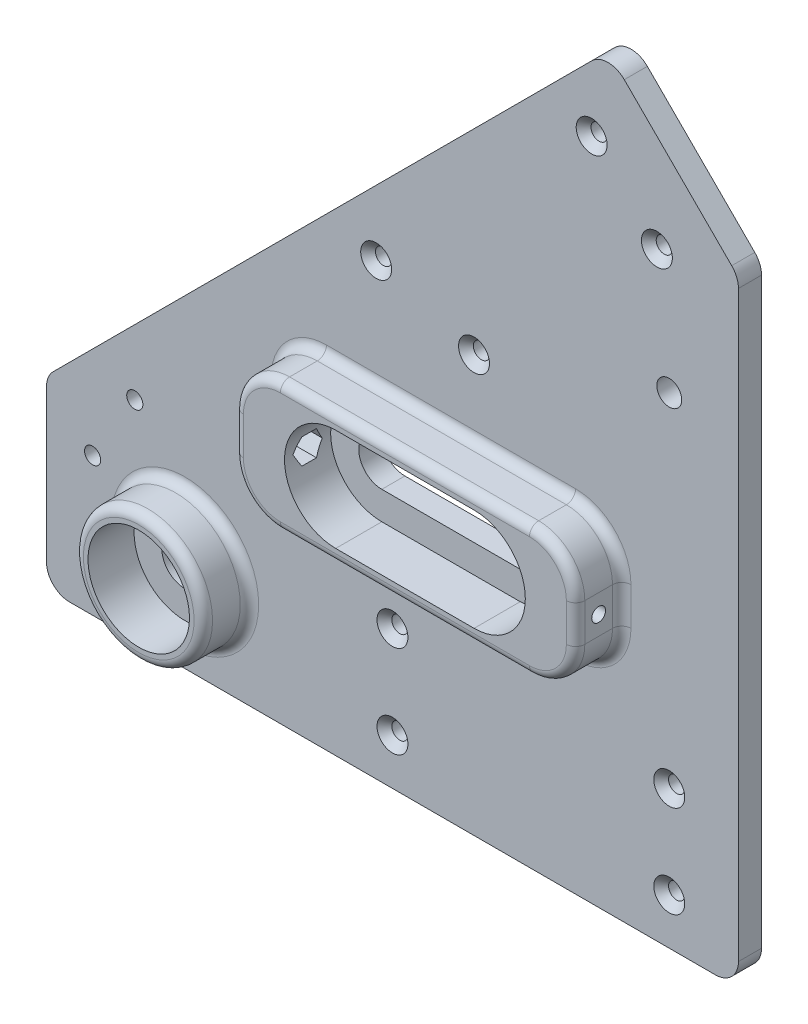
SolidWorks part; units mm, degrees
ref_plane "Front Plane" through (0, 0, 0) normal (0, 0, 1) x (1, 0, 0)
ref_plane "Top Plane" through (0, 0, 0) normal (0, 1, 0) x (1, 0, 0)
ref_plane "Right Plane" through (0, 0, 0) normal (1, 0, 0) x (0, 0, -1)
sketch "Sketch1" plane through (0, 0, 0) normal (0, 0, 1) x (1, 0, 0)
  line L0 (-75, 20) -> (46.7157, 141.7157)
  line L1 (-18.4315, 20) -> (75, 20) construction
  line L2 (-75, 20) -> (-75, -20)
  line L3 (-75, -20) -> (75, -20)
  line L4 (75, 20) -> (75, -20)
  line L5 (-75, 20) -> (75, -20) construction
  line L6 (-75, -20) -> (75, 20) construction
  line L7 (-75, -20) -> (75, -20)
  line L11 (46.7157, 141.7157) -> (75, 113.4315)
  line L12 (75, 113.4315) -> (-18.4315, 20) construction
  line L13 (-75, 0) -> (75, 0) construction
  line L14 (-75, 10) -> (75, 10) construction
  line L15 (-75, -10) -> (75, -10) construction
  line L16 (60.8579, 127.5736) -> (-46.7157, 20) construction
  line L17 (-75, 20) -> (-18.4315, 20) construction
  line L18 (53.7868, 134.6447) -> (-60.8579, 20) construction
  line L19 (67.9289, 120.5025) -> (-32.5736, 20) construction
  line L20 (75, 113.4315) -> (75, 20)
  line L21 (43.1802, 124.0381) -> (57.3223, 109.8959) construction
  line L22 (60, -10) -> (60, 10) construction
  line L23 (-65, -10) -> (-65, 10) construction
  line L24 (-2.3053, 40) -> (27.6947, 40) construction
  line L25 (-2.3053, 45) -> (27.6947, 45)
  line L26 (-2.3053, 35) -> (27.6947, 35)
  line L27 (60, 10) -> (60, 98.4315) construction
  circle A0 centre (-45, 0) radius 5
  circle A1 centre (12.6947, 40) radius 5 construction
  circle A2 centre (-65, -10) radius 1.75
  circle A3 centre (0, 10) radius 1.75
  circle A4 centre (60, -10) radius 1.75
  circle A5 centre (-55.8579, 25) radius 1.75
  circle A6 centre (43.1802, 124.0381) radius 1.75
  circle A8 centre (-27.5736, 25) radius 1.75
  circle A9 centre (57.3223, 109.8959) radius 1.75
  circle A10 centre (12.6947, 40) radius 4 construction
  circle A11 centre (-3.5355, 77.3223) radius 1.75
  circle A12 centre (17.6777, 70.2513) radius 1.75
  circle A13 centre (60, 10) radius 1.75
  circle A14 centre (-65, 10) radius 1.75
  circle A15 centre (0, -10) radius 1.75
  arc A16 (-2.3053, 45) -> (-2.3053, 35) centre (-2.3053, 40) ccw
  arc A17 (27.6947, 35) -> (27.6947, 45) centre (27.6947, 40) ccw
  circle A18 centre (60, 84.2893) radius 2.7
  point P0 (0, 0)
  point P50 (12.6947, 40)
  dimension "D8" = 10
  dimension "D11" = 10
  dimension "D12" = 3.5
  dimension "D17" = 30
  dimension "D18" = 5.4
  dimension "D1" = 40
  dimension "D2" = 40
  dimension "D3" = 45
  dimension "D4" = 10
  dimension "D5" = 10
  dimension "D6" = 10
  dimension "D7" = 10
  dimension "D9" = 30
  dimension "D10" = 150
  dimension "D13" = 10
  dimension "D14" = 15
  dimension "D15" = 5
  dimension "D16" = 15
  dimension "D19" = 10
extrude "Boss-Extrude1" add sketch "Sketch1" along normal blind 5 contours L20 L11 L0 L2 L3 L4 A0
sketch "Sketch2" plane through (0, 0, 5) normal (0, 0, 1) x (1, 0, 0)
  line L3 (-2.3053, 40) -> (27.6947, 40) construction
  line L4 (-2.3053, 51.1) -> (27.6947, 51.1)
  line L5 (-2.3053, 28.9) -> (27.6947, 28.9)
  line L6 (-24.3053, 54.1) -> (49.6947, 54.1)
  line L7 (-24.3053, 54.1) -> (-24.3053, 25.9)
  line L8 (-24.3053, 25.9) -> (49.6947, 25.9)
  line L9 (49.6947, 54.1) -> (49.6947, 25.9)
  line L10 (-24.3053, 54.1) -> (49.6947, 25.9) construction
  line L11 (-24.3053, 25.9) -> (49.6947, 54.1) construction
  circle A0 centre (-45, 0) radius 11
  circle A1 centre (-45, 0) radius 14
  circle A2 centre (12.6947, 40) radius 11.1 construction
  circle A3 centre (12.6947, 40) radius 14 construction
  arc A6 (-2.3053, 51.1) -> (-2.3053, 28.9) centre (-2.3053, 40) ccw
  arc A7 (27.6947, 28.9) -> (27.6947, 51.1) centre (27.6947, 40) ccw
  point P19 (12.6947, 40)
  dimension "D1" = 22
  dimension "D2" = 28
  dimension "D3" = 22.2
  dimension "D4" = 28
  dimension "D5" = 3
  dimension "D6" = 22
extrude "Boss-Extrude2" add sketch "Sketch2" along normal blind 10
chamfer "Chamfer1" distance 1.6 angle 45 9 edges at (-25.8236, 25, 5) (61.75, -10, 5) (61.75, 10, 5) (1.75, -10, 5) (1.75, 10, 5) (19.4277, 70.2513, 5) (-1.7855, 77.3223, 5) (59.0723, 109.8959, 5) (44.9302, 124.0381, 5)
fillet "Fillet1" radius 10 4 edges at (49.6947, 25.9, 10) (49.6947, 54.1, 10) (-24.3053, 25.9, 10) (-24.3053, 54.1, 10)
sketch "Sketch3" plane through (-24.3053, 0, 0) normal (-1, 0, 0) x (0, 0, 1)
  line L0 (10, 44.1) -> (10, 35.9) construction
  line L1 (15, 44.1) -> (5, 44.1) construction
  line L2 (5, 35.9) -> (15, 35.9) construction
  circle A0 centre (10, 40) radius 1.5
  dimension "D1" = 3
extrude "Cut-Extrude1" cut sketch "Sketch3" against normal through all
ref_plane "Plane1" through (-13.4053, 0, 0) normal (1, 0, 0) x (0, 0, -1)
sketch "Sketch4" plane through (-13.4053, 0, 0) normal (1, 0, 0) x (0, 0, -1)
  line L1 (-6.8246, 40) -> (-8.4123, 42.75)
  line L2 (-8.4123, 42.75) -> (-11.5877, 42.75)
  line L3 (-11.5877, 42.75) -> (-13.1754, 40)
  line L4 (-13.1754, 40) -> (-11.5877, 37.25)
  line L5 (-11.5877, 37.25) -> (-8.4123, 37.25)
  line L6 (-8.4123, 37.25) -> (-6.8246, 40)
  circle A0 centre (-10, 40) radius 2.75 construction
  dimension "D1" = 5.5
extrude "Cut-Extrude3" cut sketch "Sketch4" against normal blind 5 and the other way offset from surface (57.1 mm away) 6 other way up to face at (49.6947, 38.5, 10)
fillet "Fillet2" radius 2 9 edges at (46.7658, 51.1711, 5) (49.6947, 40, 5) (46.7658, 28.8289, 5) (12.6947, 25.9, 5) (-21.3764, 28.8289, 5) (-24.3053, 40, 5) (-21.3764, 51.1711, 5) (-31, 0, 5) (12.6947, 54.1, 5)
fillet "Fillet3" radius 2 9 edges at (46.7658, 51.1711, 15) (49.6947, 40, 15) (46.7658, 28.8289, 15) (12.6947, 25.9, 15) (-21.3764, 28.8289, 15) (-24.3053, 40, 15) (-21.3764, 51.1711, 15) (-31, 0, 15) (12.6947, 54.1, 15)
fillet "Fillet4" radius 5 5 edges at (75, 113.4315, 2.5) (46.7157, 141.7157, 2.5) (75, -20, 2.5) (-75, -20, 2.5) (-75, 20, 2.5)
